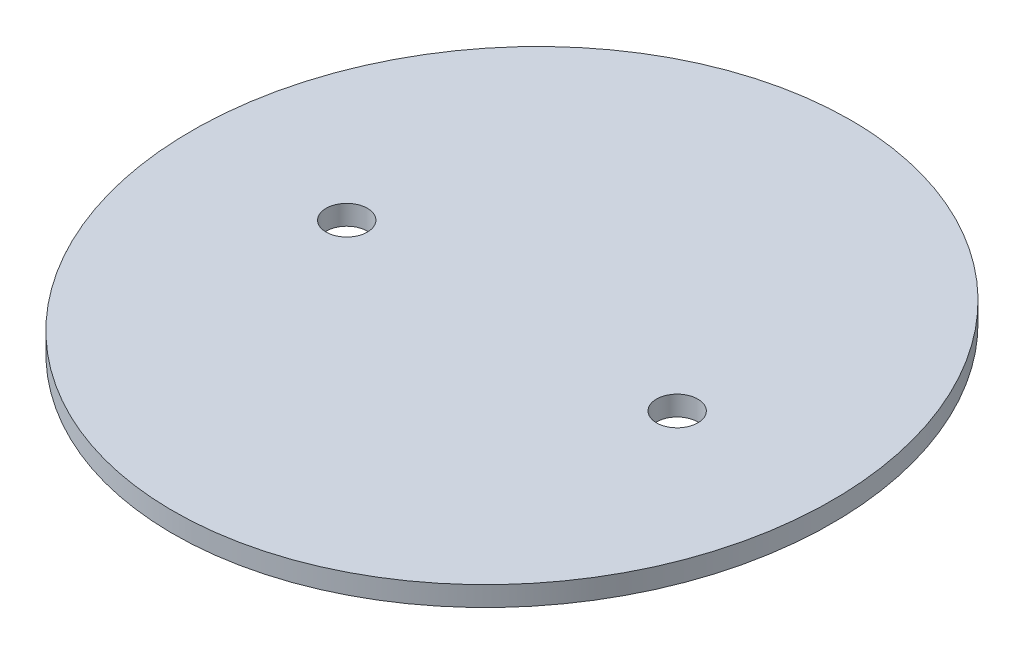
SolidWorks part; units mm, degrees
ref_plane "Front Plane" through (0, 0, 0) normal (0, 0, 1) x (1, 0, 0)
ref_plane "Top Plane" through (0, 0, 0) normal (0, 1, 0) x (1, 0, 0)
ref_plane "Right Plane" through (0, 0, 0) normal (1, 0, 0) x (0, 0, -1)
sketch "Sketch1" plane through (0, 0, 0) normal (0, 1, 0) x (1, 0, 0)
  circle A0 centre (-50, 0) radius 6.25
  circle A1 centre (50, 0) radius 6.25
  ellipse E0 centre (0, 0) end of major axis (0, 102.5) minor radius 96.9
  dimension "D3" = 12.5
  dimension "D1" = 205
  dimension "D2" = 193.8
  dimension "D4" = 100
  dimension "D5" = 50
extrude "Boss-Extrude1" add sketch "Sketch1" along normal blind 6
